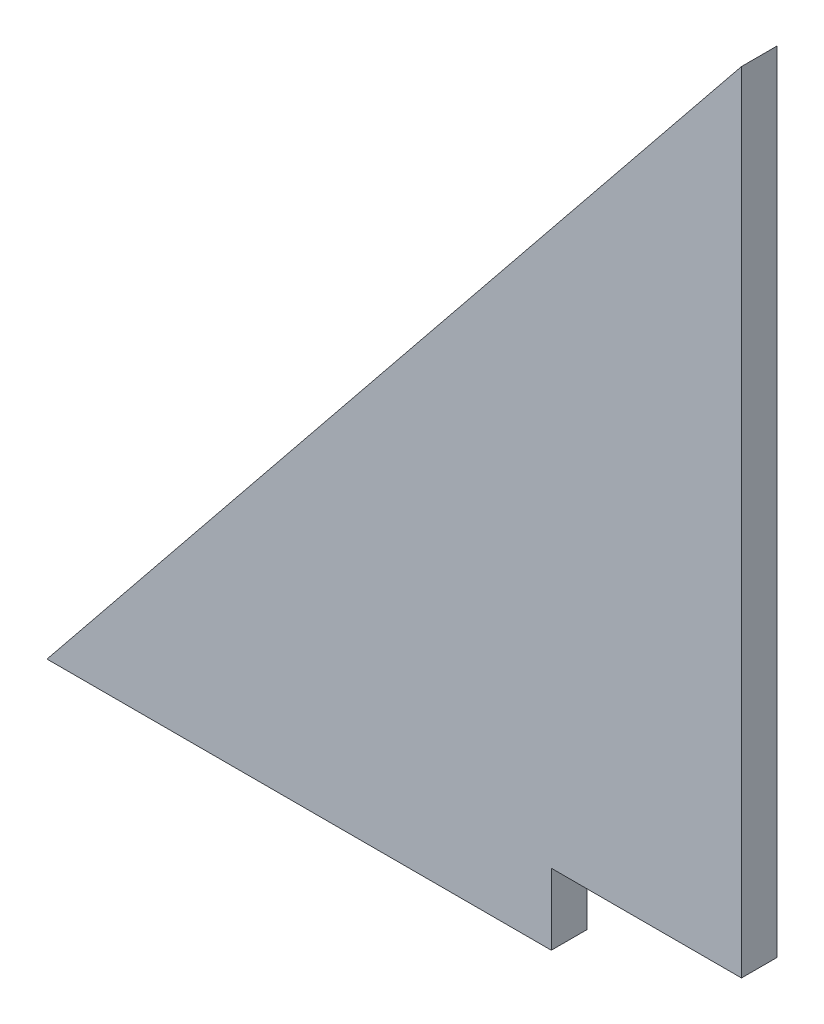
SolidWorks part; units mm, degrees
ref_plane "Front Plane" through (0, 0, 0) normal (0, 0, 1) x (1, 0, 0)
ref_plane "Top Plane" through (0, 0, 0) normal (0, 1, 0) x (1, 0, 0)
ref_plane "Right Plane" through (0, 0, 0) normal (1, 0, 0) x (0, 0, -1)
sketch "Sketch1" plane through (0, 0, 0) normal (0, 0, 1) x (1, 0, 0)
  line L15 (-16.827, -36.9367) -> (-16.9215, -36.9367)
  line L16 (-16.9215, -36.9367) -> (-16.9215, -43.2883)
  line L17 (-16.9215, -43.2883) -> (-62, -43.2883)
  line L19 (0.078, -36.9367) -> (0.078, 33.6228)
  line L20 (0.078, 33.6228) -> (-62, -43.2883)
  line L21 (-16.827, -36.9367) -> (0.078, -36.9367)
  dimension "D1" = 6.3515
  dimension "D2" = 16.9995
  dimension "D3" = 45.0785
  dimension "D4" = 70.5596
extrude "Boss-Extrude1" add sketch "Sketch1" along normal blind 3.175
